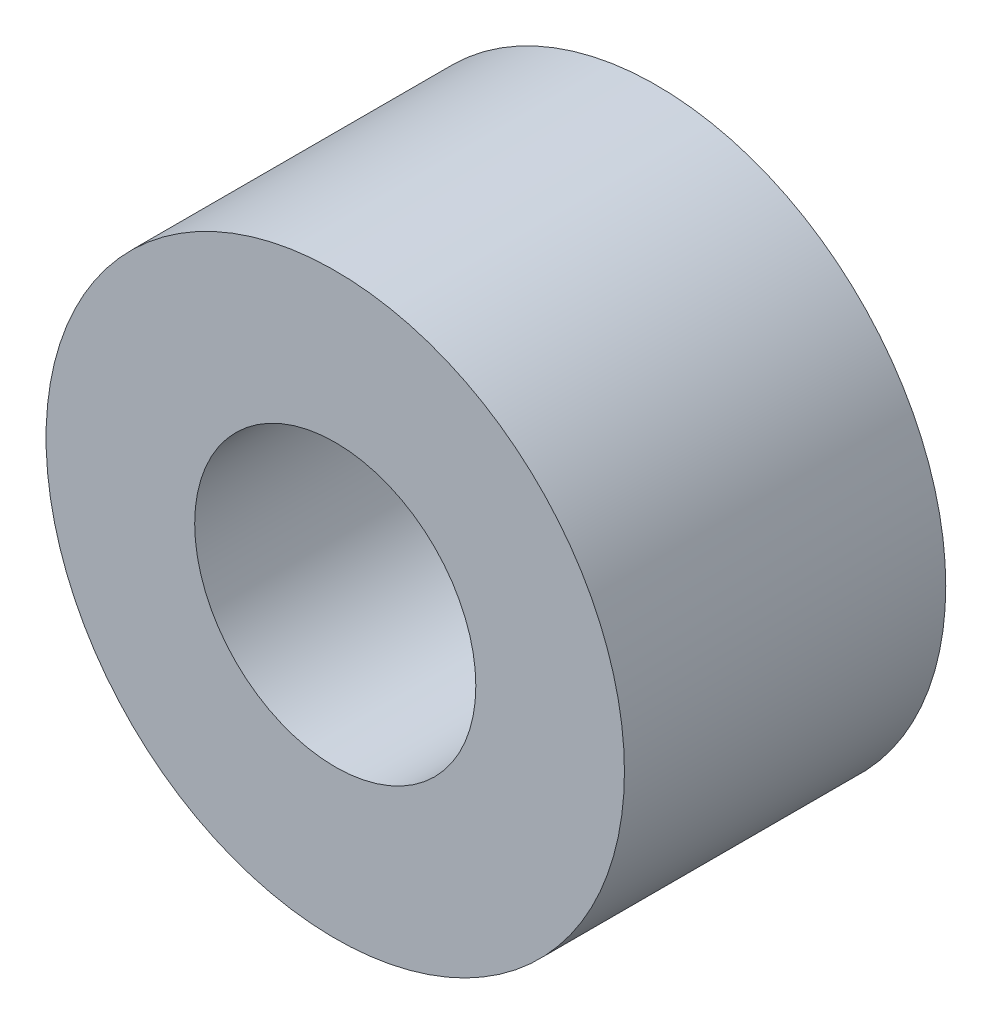
SolidWorks part; units mm, degrees
material "AISI 1020"
ref_plane "Спереди" through (0, 0, 0) normal (0, 0, 1) x (1, 0, 0)
ref_plane "Сверху" through (0, 0, 0) normal (0, 1, 0) x (1, 0, 0)
ref_plane "Справа" through (0, 0, 0) normal (1, 0, 0) x (0, 0, -1)
sketch "Эскиз1" plane through (0, 0, 0) normal (0, 0, 1) x (1, 0, 0)
  line L0 (18, -16) -> (18, 16) construction
  circle A0 centre (0, 0) radius 18
extrude "Бобышка-Вытянуть1" add sketch "Эскиз1" along normal blind 20
hole_wizard "Отверстие обработанное метчиком M201" positions "Эскиз2" profile "Эскиз3" tap size "M20" standard "ISO"
sketch "Эскиз2" plane through (0, 0, 0) normal (0, 0, -1) x (-1, 0, 0)
  point P0 (0, 0)
sketch "Эскиз3" plane through (0, 0, 0) normal (1, 0, 0) x (0, 1, 0)
  line L0 (0, 0) -> (0, 57.7575)
  line L1 (0, 57.7575) -> (8.75, 52.5)
  line L2 (8.75, 52.5) -> (8.75, 0)
  line L5 (8.75, 0) -> (0, 0)
  line L10 (0, 57.7575) -> (-8.75, 52.5) construction
  line L11 (0, -6.35) -> (0, 107.95) construction
  dimension "Диаметр сверла" = 17.5
  dimension "Глубина сверла" = 52.5
  dimension "Угол заточки сверла" = 118
cosmetic thread "Отверстие резьбы1" parameters "D1"=20, "D2"=20
